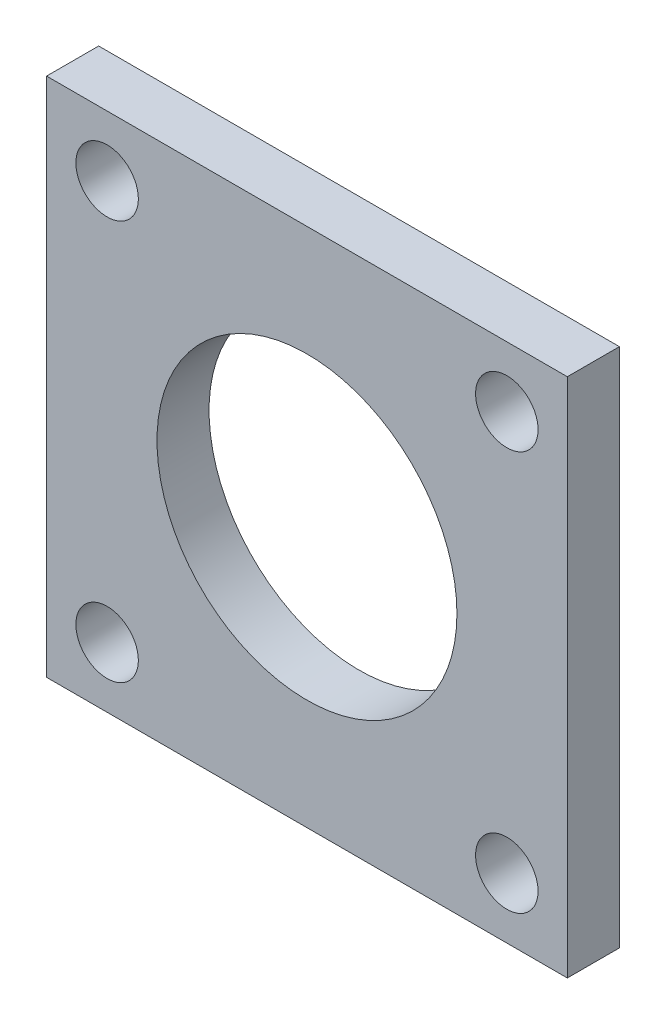
SolidWorks part; units mm, degrees
ref_plane "Front Plane" through (0, 0, 0) normal (0, 0, 1) x (1, 0, 0)
ref_plane "Top Plane" through (0, 0, 0) normal (0, 1, 0) x (1, 0, 0)
ref_plane "Right Plane" through (0, 0, 0) normal (1, 0, 0) x (0, 0, -1)
sketch "Sketch1" plane through (0, 0, 0) normal (0, 0, 1) x (1, 0, 0)
  line L1 (-12.7, -12.7) -> (12.7, -12.7)
  line L2 (-12.7, -12.7) -> (-12.7, 12.7)
  line L3 (-12.7, 12.7) -> (12.7, 12.7)
  line L4 (12.7, -12.7) -> (12.7, 12.7)
  line L5 (-12.7, -12.7) -> (12.7, 12.7) construction
  line L6 (-12.7, 12.7) -> (12.7, -12.7) construction
  circle A0 centre (0, 0) radius 7.3152
  circle A1 centre (9.7484, 9.7484) radius 1.524
  circle A2 centre (-9.7484, -9.7484) radius 1.524
  circle A3 centre (9.7484, -9.7484) radius 1.524
  circle A4 centre (-9.7484, 9.7484) radius 1.524
  point P29 (0, 0)
  point P30 (0, 0)
  point P31 (0, 0)
  point P32 (0, 0)
  point P33 (0, 0)
  point P34 (0, 0)
  point P35 (0, 0)
  point P36 (0, 0)
  point P37 (0, 0)
  point P38 (0, 0)
  point P39 (0, 0)
  point P40 (0, 0)
  point P41 (0, 0)
  point P42 (0, 0)
  point P43 (0, 0)
  point P44 (28.5848, 0)
extrude "Boss-Extrude6" add sketch "Sketch1" along normal blind 2.54
